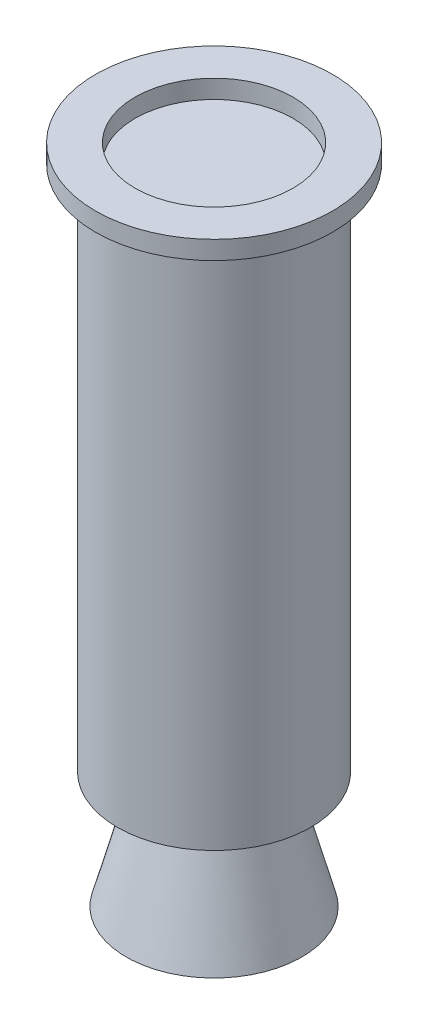
SolidWorks part; units mm, degrees
ref_plane "Front Plane" through (0, 0, 0) normal (0, 0, 1) x (1, 0, 0)
ref_plane "Top Plane" through (0, 0, 0) normal (0, 1, 0) x (1, 0, 0)
ref_plane "Right Plane" through (0, 0, 0) normal (1, 0, 0) x (0, 0, -1)
sketch "Sketch1" plane through (0, 0, 0) normal (0, 0, 1) x (1, 0, 0)
  line L0 (0, 0) -> (-38.1, 0)
  line L3 (-38.1, 0) -> (-38.1, -157.332)
  line L5 (-38.1, -157.332) -> (-19.3311, -208.1132)
  line L10 (-17.8883, -219.2048) -> (-41.656, -307.594)
  line L12 (-41.656, -307.594) -> (0, -307.594)
  line L13 (0, 0) -> (0, -307.594)
  arc A0 (-19.3311, -208.1132) -> (-17.653, -217.424) centre (-44.7122, -217.4941) cw
  arc A1 (-17.653, -217.424) -> (-17.8883, -219.2048) centre (-24.379, -217.4414) cw
  dimension "D3" = 27.0593
  dimension "D4" = 6.726
  dimension "D1" = 38.1
  dimension "D2" = 157.332
  dimension "D5" = 41.656
  dimension "D6" = 74.949
revolve "CHAMBER GEOMETRY" add sketch "Sketch1" angle 360 about L13
sketch "Sketch3" plane through (0, 0, 0) normal (0, 0, 1) x (1, 0, 0)
  line L0 (0, -217.424) -> (0, -157.332) construction
  line L1 (17.653, -217.424) -> (-17.653, -217.424) construction
  line L2 (38.1, -157.332) -> (-38.1, -157.332) construction
  line L3 (38.1, -157.332) -> (19.3311, -208.1132)
  line L4 (17.8883, -219.2048) -> (19.2543, -224.2848)
  line L5 (41.656, -307.594) -> (17.8883, -219.2048) construction
  line L6 (19.2543, -224.2848) -> (20.4186, -223.9718)
  line L7 (20.4186, -223.9718) -> (19.0525, -218.8918)
  line L8 (19.3311, -208.1132) -> (20.6011, -208.1132)
  line L9 (17.653, -217.424) -> (18.923, -217.424) construction
  line L10 (0, -217.424) -> (0, -219.2048) construction
  line L11 (17.8883, -219.2048) -> (-17.8883, -219.2048) construction
  line L12 (19.3311, -208.1132) -> (23.7365, -196.1939)
  line L13 (23.7365, -196.1939) -> (24.9277, -196.6342)
  line L14 (20.6011, -208.1132) -> (24.9277, -196.6342)
  line L15 (19.3311, -208.1132) -> (20.6011, -208.1132)
  line L16 (19.3311, -208.1132) -> (23.7365, -196.1939)
  line L17 (24.9277, -196.6342) -> (39.454, -157.332)
  line L18 (39.454, -157.332) -> (38.1, -157.332)
  line L19 (39.454, -157.332) -> (39.454, -132.0037)
  line L20 (39.454, -132.0037) -> (37.9846, -132.0037)
  line L21 (37.9846, -132.0037) -> (38.1, -157.332)
  arc A0 (19.3311, -208.1132) -> (17.653, -217.424) centre (44.7122, -217.4941) ccw
  arc A1 (17.653, -217.424) -> (17.8883, -219.2048) centre (24.379, -217.4414) ccw
  arc A2 (19.0525, -218.8918) -> (18.923, -217.424) centre (23.1469, -217.7908) cw
  arc A6 (18.923, -217.424) -> (20.6011, -208.1132) centre (70.393, -221.8936) cw
  dimension "D1" = 5.08
  dimension "D2" = 5.08
  dimension "D6" = 27.0593
  dimension "D7" = 1.27
  dimension "D5" = 1.27
  dimension "D3" = 1.2056
  dimension "D4" = 1.27
  dimension "D8" = 11.479
  dimension "D9" = 1.4694
  dimension "D10" = 25.3283
revolve "CF REVOLVE" add sketch "Sketch3" angle 360 about L0
sketch "Sketch4" plane through (0, 0, 0) normal (0, 0, 1) x (1, 0, 0)
  line L0 (0, -217.424) -> (0, -218.8918) construction
  line L1 (18.923, -217.424) -> (-18.923, -217.424) construction
  line L2 (19.0525, -218.8918) -> (-19.0525, -218.8918) construction
  line L3 (0, -218.1579) -> (18.9235, -218.1636) construction
  line L4 (18.9235, -218.1636) -> (18.9235, -213.0836)
  line L5 (18.9235, -218.1636) -> (18.9235, -221.2116)
  line L6 (18.9235, -213.0836) -> (20.9555, -213.0836)
  line L7 (20.9555, -213.0836) -> (20.9555, -221.2116)
  line L8 (20.9555, -221.2116) -> (18.9235, -221.2116)
  arc A0 (18.923, -217.424) -> (19.0525, -218.8918) centre (23.1469, -217.7908) ccw construction
  dimension "D1" = 5.08
  dimension "D2" = 3.048
  dimension "D3" = 2.032
revolve "RTV/EPOXY" add sketch "Sketch4" angle 360 about L0
sketch "Sketch6" plane through (0, 0, 0) normal (0, 0, 1) x (1, 0, 0)
  line L0 (0, -307.594) -> (0, -224.2848) construction
  line L1 (-41.656, -307.594) -> (41.656, -307.594) construction
  line L2 (19.2543, -224.2848) -> (-19.2543, -224.2848) construction
  line L3 (41.656, -307.594) -> (21.8705, -234.0144)
  line L4 (41.656, -307.594) -> (19.2543, -224.2848) construction
  line L5 (21.8705, -234.0144) -> (-21.8705, -234.0144)
  line L6 (-19.2543, -224.2848) -> (-41.656, -307.594) construction
  line L7 (-21.8705, -234.0144) -> (-41.656, -307.594)
  line L8 (-41.656, -307.594) -> (41.656, -307.594)
  dimension "D1" = 43.7411
extrude "Cut-Extrude1" cut sketch "Sketch6" against normal through all both and the other way through all
sketch "Sketch7" plane through (0, 0, 0) normal (1, 0, 0) x (0, 0, -1)
  line L0 (-21.8705, -234.0144) -> (-42.3595, -310.2144)
  line L1 (-21.8705, -234.0144) -> (21.8705, -234.0144) construction
  line L2 (-42.3595, -310.2144) -> (0, -310.2144)
  line L3 (0, -310.2144) -> (0, -234.0144)
  line L4 (0, -234.0144) -> (-21.8705, -234.0144)
  dimension "D1" = 76.2
  dimension "D2" = 105.05
revolve "DASHED RTV/EPOXY" add sketch "Sketch7" angle 360 about L3
sketch "Sketch10" plane through (0, 0, 0) normal (0, 0, 1) x (1, 0, 0)
  line L0 (39.454, -157.332) -> (34.76, -170.032)
  line L1 (24.9277, -196.6342) -> (39.454, -157.332) construction
  line L2 (34.76, -170.032) -> (34.76, -250.042)
  line L3 (21.8705, -234.0144) -> (26.1801, -250.042)
  line L4 (42.3595, -310.2144) -> (21.8705, -234.0144) construction
  line L5 (26.1801, -250.042) -> (34.76, -250.042)
  line L6 (21.8705, -234.0144) -> (21.8705, -204.7451)
  line L7 (20.6011, -208.1132) -> (24.9277, -196.6342) construction
  line L8 (21.8705, -204.7451) -> (34.76, -170.032)
  line L9 (0, -221.2116) -> (0, -213.0836) construction
  line L10 (-19.6763, -221.2116) -> (19.6763, -221.2116) construction
  line L11 (20.9555, -213.0836) -> (-20.9555, -213.0836) construction
  dimension "D1" = 12.7
  dimension "D2" = 80.01
revolve "DASHED RTV/EPOXY OVERHANG" add sketch "Sketch10" angle 360 about L9
sketch "Sketch11" plane through (0, 0, 0) normal (0, 0, 1) x (1, 0, 0)
  line L1 (34.76, -253.9479) -> (27.2303, -253.9479)
  line L2 (42.3595, -310.2144) -> (26.1801, -250.042) construction
  line L4 (-34.76, -250.042) -> (34.76, -250.042) construction
  line L5 (27.2303, -250.042) -> (34.76, -250.042)
  line L6 (34.76, -253.9479) -> (46.5848, -253.9479)
  line L7 (46.5848, -253.9479) -> (46.5848, 0)
  line L8 (46.5848, 0) -> (57.15, 0)
  line L9 (57.15, 0) -> (57.15, 8.89)
  line L10 (38.1, 0) -> (38.1, 8.89)
  line L11 (38.1, 8.89) -> (57.15, 8.89)
  line L12 (38.1, 0) -> (38.1, -132.0037)
  line L16 (38.1, -250.042) -> (34.76, -250.042)
  line L17 (0, 0) -> (0, -132.0037) construction
  line L18 (39.454, -132.0037) -> (-39.454, -132.0037) construction
  line L19 (38.1, -132.0037) -> (38.1, -250.042)
  line L20 (27.2303, -250.042) -> (25.2827, -250.042)
  line L21 (-26.1801, -250.042) -> (26.1801, -250.042) construction
  line L22 (25.2827, -250.042) -> (25.2827, -253.9479)
  line L23 (25.2827, -253.9479) -> (27.2303, -253.9479)
  dimension "D1" = 7.5297
  dimension "D2" = 3.9058
  dimension "D3" = 8.89
  dimension "D4" = 19.05
  dimension "D5" = 11.8248
  dimension "D6" = 1.9477
  dimension "D7" = 3.9058
revolve "BLUE TUBE" add sketch "Sketch11" angle 360 about L17
